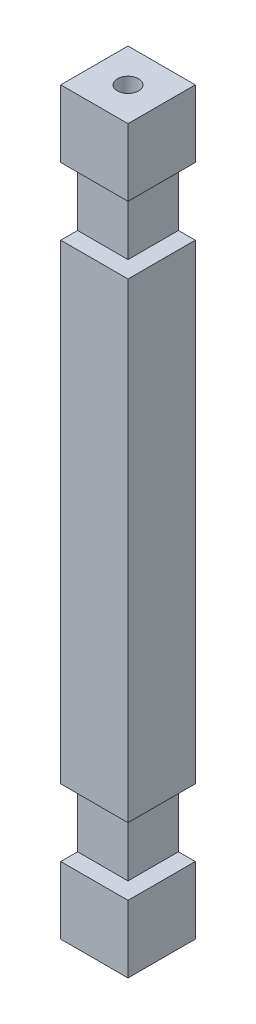
SolidWorks part; units mm, degrees
material "Balsa"
ref_plane "Front Plane" through (0, 0, 0) normal (0, 0, 1) x (1, 0, 0)
ref_plane "Top Plane" through (0, 0, 0) normal (0, 1, 0) x (1, 0, 0)
ref_plane "Right Plane" through (0, 0, 0) normal (1, 0, 0) x (0, 0, -1)
sketch "Sketch2" plane through (0, 0, 0) normal (0, 0, 1) x (1, 0, 0)
  line L0 (25.4, -279.4) -> (-25.4, 279.4) construction
  line L1 (-25.4, 279.4) -> (25.4, 279.4)
  line L2 (-25.4, 279.4) -> (-25.4, -279.4)
  line L3 (-25.4, -279.4) -> (25.4, -279.4)
  line L4 (25.4, 279.4) -> (25.4, -279.4)
  line L5 (25.4, 279.4) -> (-25.4, -279.4) construction
  dimension "D1" = 50.8
  dimension "D2" = 558.8
extrude "Boss-Extrude1" add sketch "Sketch2" along normal blind 50.8
sketch "Sketch5" plane through (0, 0, 50.8) normal (0, 0, 1) x (1, 0, 0)
  line L0 (-25.4, 279.4) -> (-25.4, -279.4) construction
  line L1 (-25.4, 228.6) -> (25.4, 228.6)
  line L2 (-25.4, 228.6) -> (-25.4, 177.8)
  line L3 (-25.4, 177.8) -> (25.4, 177.8)
  line L4 (25.4, 228.6) -> (25.4, 177.8)
  line L5 (25.4, -279.4) -> (25.4, 279.4) construction
  line L6 (25.4, 279.4) -> (-25.4, 279.4) construction
  dimension "D1" = 50.8
  dimension "D2" = 50.8
extrude "Cut-Extrude1" cut sketch "Sketch5" against normal blind 12.7
sketch "Sketch6" plane through (25.4, 0, 0) normal (1, 0, 0) x (0, 0, -1)
  line L0 (0, -279.4) -> (0, 279.4) construction
  line L1 (-50.8, 228.6) -> (0, 228.6)
  line L2 (-50.8, 228.6) -> (-50.8, 177.8)
  line L3 (-50.8, 177.8) -> (0, 177.8)
  line L4 (0, 228.6) -> (0, 177.8)
  dimension "D1" = 50.8
extrude "Cut-Extrude2" cut sketch "Sketch6" against normal blind 12.7
sketch "Sketch10" plane through (0, 0, 50.8) normal (0, 0, 1) x (1, 0, 0)
  line L0 (25.4, -279.4) -> (25.4, 177.8) construction
  line L1 (25.4, -177.8) -> (-25.4, -177.8)
  line L2 (25.4, -177.8) -> (25.4, -228.6)
  line L3 (25.4, -228.6) -> (-25.4, -228.6)
  line L4 (-25.4, -177.8) -> (-25.4, -228.6)
  line L5 (-25.4, 177.8) -> (-25.4, -279.4) construction
  line L6 (-25.4, -279.4) -> (25.4, -279.4) construction
  dimension "D1" = 50.8
  dimension "D2" = 50.8
extrude "Cut-Extrude3" cut sketch "Sketch10" against normal blind 12.7
sketch "Sketch11" plane through (25.4, 0, 0) normal (1, 0, 0) x (0, 0, -1)
  line L0 (0, -279.4) -> (0, 177.8) construction
  line L1 (-50.8, -177.8) -> (0, -177.8)
  line L2 (-50.8, -177.8) -> (-50.8, -228.6)
  line L3 (-50.8, -228.6) -> (0, -228.6)
  line L4 (0, -177.8) -> (0, -228.6)
  dimension "D1" = 50.8
extrude "Cut-Extrude4" cut sketch "Sketch11" against normal blind 12.7
sketch "Sketch12" plane through (0, -279.4, 0) normal (0, -1, 0) x (1, 0, 0)
  line L0 (-25.4, 0) -> (25.4, 0) construction
  line L1 (-25.4, 50.8) -> (-25.4, 0) construction
  circle A0 centre (0, 25.4) radius 8
  dimension "D1" = 16
  dimension "D2" = 25.4
  dimension "D3" = 25.4
extrude "Cut-Extrude5" cut sketch "Sketch12" against normal blind 16
sketch "Sketch13" plane through (0, 279.4, 0) normal (0, 1, 0) x (1, 0, 0)
  line L0 (25.4, -50.8) -> (25.4, 0) construction
  line L1 (25.4, 0) -> (-25.4, 0) construction
  circle A0 centre (0, -25.4) radius 8
  dimension "D1" = 16
  dimension "D2" = 25.4
  dimension "D3" = 25.4
extrude "Cut-Extrude6" cut sketch "Sketch13" against normal blind 16
